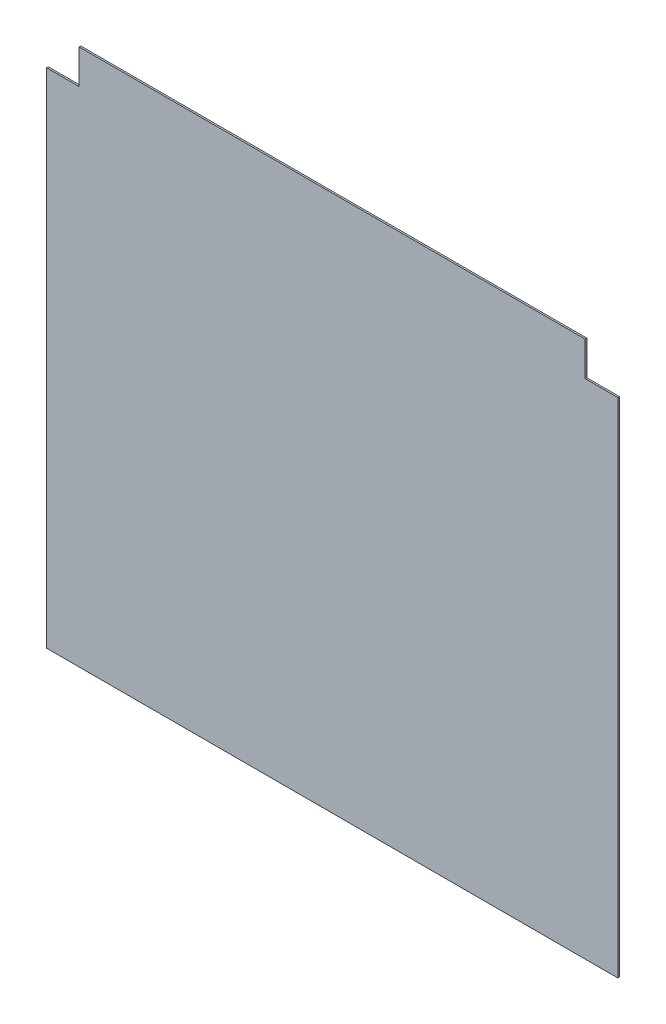
SolidWorks part; units mm, degrees
ref_plane "정면" through (0, 0, 0) normal (0, 0, 1) x (1, 0, 0)
ref_plane "윗면" through (0, 0, 0) normal (0, 1, 0) x (1, 0, 0)
ref_plane "우측면" through (0, 0, 0) normal (1, 0, 0) x (0, 0, -1)
sketch "스케치1" plane through (0, 0, 0) normal (0, 0, 1) x (1, 0, 0)
  line L0 (0, 0) -> (350, 0)
  line L1 (350, 0) -> (350, 308)
  line L2 (350, 308) -> (330, 308)
  line L3 (330, 308) -> (330, 329)
  line L4 (330, 329) -> (20, 329)
  line L5 (20, 329) -> (20, 308)
  line L6 (20, 308) -> (0, 308)
  line L7 (0, 308) -> (0, 0)
  dimension "D1" = 310
  dimension "D2" = 308
  dimension "D3" = 21
  dimension "D4" = 20
  dimension "D5" = 21
  dimension "D6" = 20
extrude "보스-돌출1" add sketch "스케치1" along normal blind 1 contours L4 L5 L6 L7 L0 L1 L2 L3
